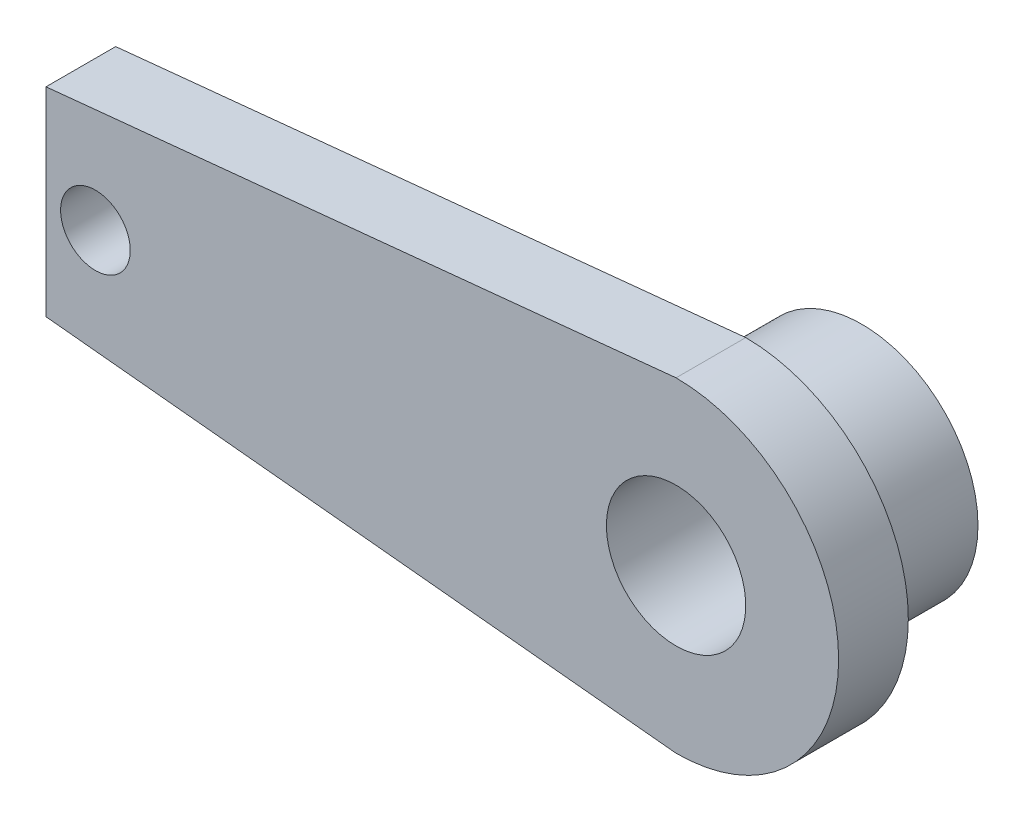
SolidWorks part; units mm, degrees
ref_plane "Front Plane" through (0, 0, 0) normal (0, 0, 1) x (1, 0, 0)
ref_plane "Top Plane" through (0, 0, 0) normal (0, 1, 0) x (1, 0, 0)
ref_plane "Right Plane" through (0, 0, 0) normal (1, 0, 0) x (0, 0, -1)
sketch "Sketch1" plane through (0, 0, 0) normal (0, 0, 1) x (1, 0, 0)
  circle A0 centre (0, 0) radius 3
  circle A1 centre (0, 0) radius 5
  dimension "D1" = 6
  dimension "D2" = 10
extrude "Boss-Extrude1" add sketch "Sketch1" along normal blind 5
sketch "Sketch2" plane through (0, 0, 5) normal (0, 0, 1) x (1, 0, 0)
  line L0 (-30, 4) -> (0, 7)
  line L1 (-30, -4) -> (0, -7)
  arc A0 (0, -7) -> (0, 7) centre (0, 0) ccw
  arc A1 (-30, 4) -> (-30, -4) centre (-30, 0) ccw
  dimension "D1" = 14
  dimension "D2" = 8
  dimension "D3" = 30
extrude "Boss-Extrude2" add sketch "Sketch2" along normal blind 3
sketch "Sketch3" plane through (0, 0, 5) normal (0, 0, -1) x (-1, 0, 0)
  circle A0 centre (25, 0) radius 1.5
  dimension "D1" = 3
  dimension "D2" = 25
extrude "Cut-Extrude1" cut sketch "Sketch3" against normal blind 3
sketch "Sketch4" plane through (0, 0, 5) normal (0, 0, -1) x (-1, 0, 0)
  circle A1 centre (0, 0) radius 3
  circle A2 centre (0, 0) radius 3
  dimension "D1" = 0
extrude "Cut-Extrude2" cut sketch "Sketch4" against normal blind 3
sketch "Sketch5" plane through (0, 0, 5) normal (0, 0, -1) x (-1, 0, 0)
  line L1 (27.128, 0) -> (27.128, 4.2872)
  line L2 (0, 7) -> (30, 4) construction
  line L3 (27.128, 4.2872) -> (27.128, -4.2872)
  line L4 (30, -4) -> (0, -7) construction
  line L6 (30, 4) -> (0, 7)
  line L7 (0, -7) -> (30, -4)
  line L8 (30, 4) -> (27.128, 4.2872)
  line L9 (27.128, -4.2872) -> (30, -4)
  arc A3 (30, -4) -> (30, 4) centre (30, 0) ccw
  arc A4 (0, 7) -> (0, -7) centre (0, 0) ccw
  arc A5 (30, -4) -> (30, 4) centre (30, 0) ccw
  arc M7 (30, -4) -> (30, 4) centre (30, 0) ccw
  line M8 (30, 4) -> (0, 7)
  line M10 (0, -7) -> (30, -4)
  dimension "D1" = 0
extrude "Cut-Extrude3" cut sketch "Sketch5" against normal blind 10 contours L1 L3 M10 M7 M8
